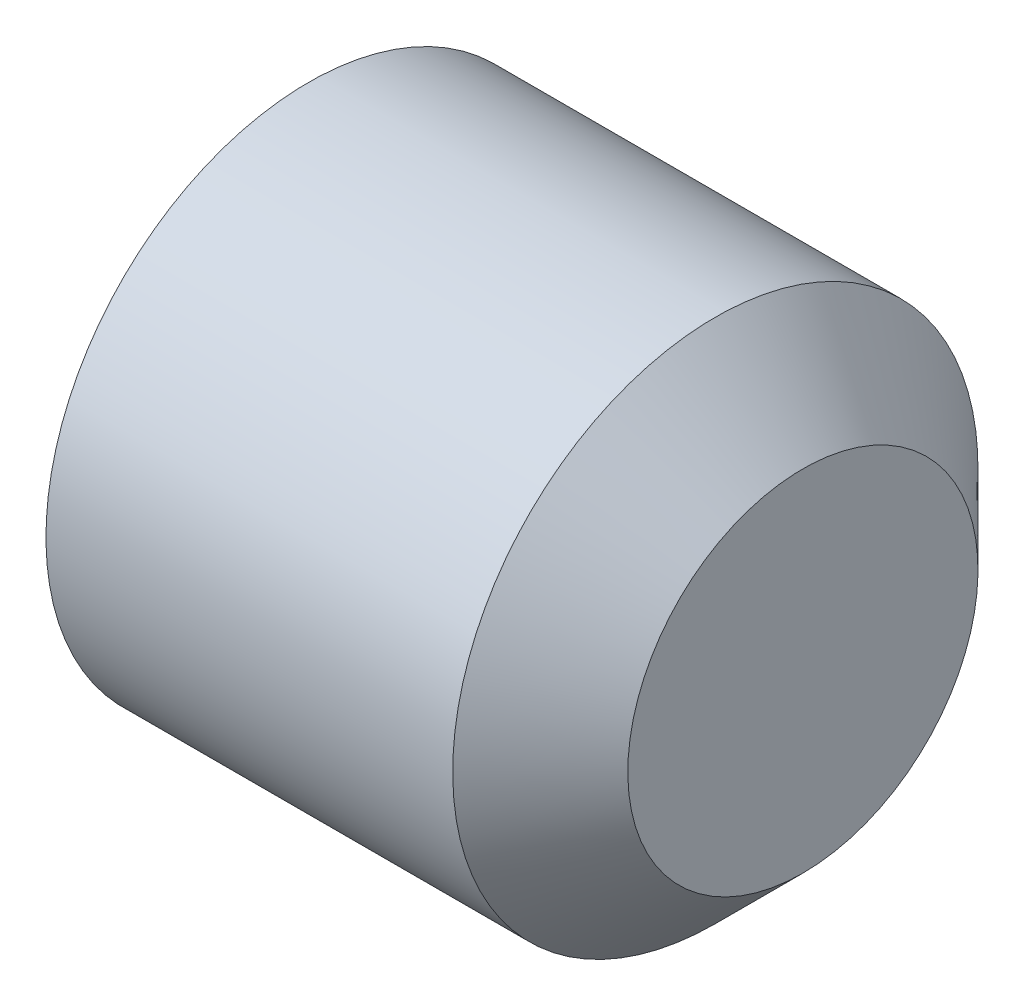
SolidWorks part; units mm, degrees
ref_plane "Front Plane" through (0, 0, 0) normal (0, 0, 1) x (1, 0, 0)
ref_plane "Top Plane" through (0, 0, 0) normal (0, 1, 0) x (1, 0, 0)
ref_plane "Right Plane" through (0, 0, 0) normal (1, 0, 0) x (0, 0, -1)
ref_plane "Plane1" through (0, 0, 0) normal (0, 0, 1) x (1, 0, 0)
sketch "Sketch1" plane through (0, 0, 0) normal (0, 0, 1) x (1, 0, 0)
  line L0 (3, 0) -> (3, -1)
  line L1 (3, -1) -> (2.5, -1.5)
  line L2 (2.5, -1.5) -> (0.177, -1.5)
  line L3 (0.177, -1.5) -> (0, -1.1935)
  line L4 (0, -1.1935) -> (0, -0.866)
  line L5 (0, -0.866) -> (0.5, 0)
  line L6 (0.5, 0) -> (3, 0)
  line L7 (0.5, 0) -> (3, 0) construction
revolve "Revolve1" add sketch "Sketch1" angle 360 about L7
ref_plane "Plane2" through (0, 0, 0) normal (1, 0, 0) x (0, 0, -1)
sketch "Sketch2" plane through (0, 0, 0) normal (1, 0, 0) x (0, 0, -1)
  line L0 (-0.866, 0) -> (-0.433, -0.75)
  line L1 (-0.433, -0.75) -> (0.433, -0.75)
  line L2 (0.433, -0.75) -> (0.866, 0)
  line L3 (0.866, 0) -> (0.433, 0.75)
  line L4 (0.433, 0.75) -> (-0.433, 0.75)
  line L5 (-0.433, 0.75) -> (-0.866, 0)
extrude "Cut-Extrude1" cut sketch "Sketch2" along normal blind 1.2
